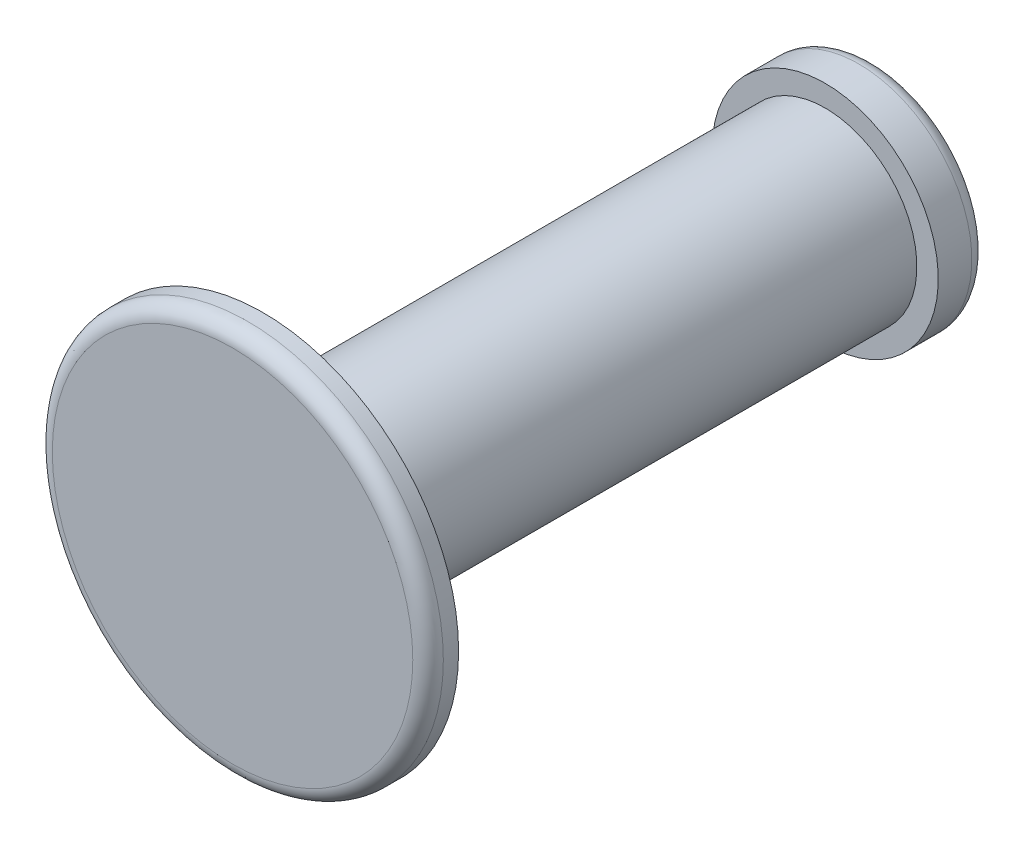
SolidWorks part; units mm, degrees
material "Zinc Alloy 7; AG40B; Zn-4Al-0.015Mg"
ref_plane "Front Plane" through (0, 0, 0) normal (0, 0, 1) x (1, 0, 0)
ref_plane "Top Plane" through (0, 0, 0) normal (0, 1, 0) x (1, 0, 0)
ref_plane "Right Plane" through (0, 0, 0) normal (1, 0, 0) x (0, 0, -1)
sketch "Sketch1" plane through (0, 0, 0) normal (0, 0, 1) x (1, 0, 0)
  circle A0 centre (0, 0) radius 0.75
  dimension "D1" = 1.5
extrude "Extrude1" add sketch "Sketch1" along normal mid plane 4.6
sketch "Sketch2" plane through (0, 0, 2.3) normal (0, 0, 1) x (1, 0, 0)
  circle A0 centre (0, 0) radius 1.6
  circle A1 centre (0, 0) radius 0.75 construction
  dimension "D1" = 3.2
extrude "Extrude2" add sketch "Sketch2" along normal blind 0.25
sketch "Sketch3" plane through (0, 0, -2.3) normal (0, 0, -1) x (-1, 0, 0)
  circle A0 centre (0, 0) radius 0.925
  circle A1 centre (0, 0) radius 0.75 construction
  dimension "D1" = 1.85
extrude "Extrude3" add sketch "Sketch3" along normal blind 0.4
fillet "Fillet1" radius 0.125 2 edges at (1.6, 0, 2.55) (-0.925, 0, -2.7)
